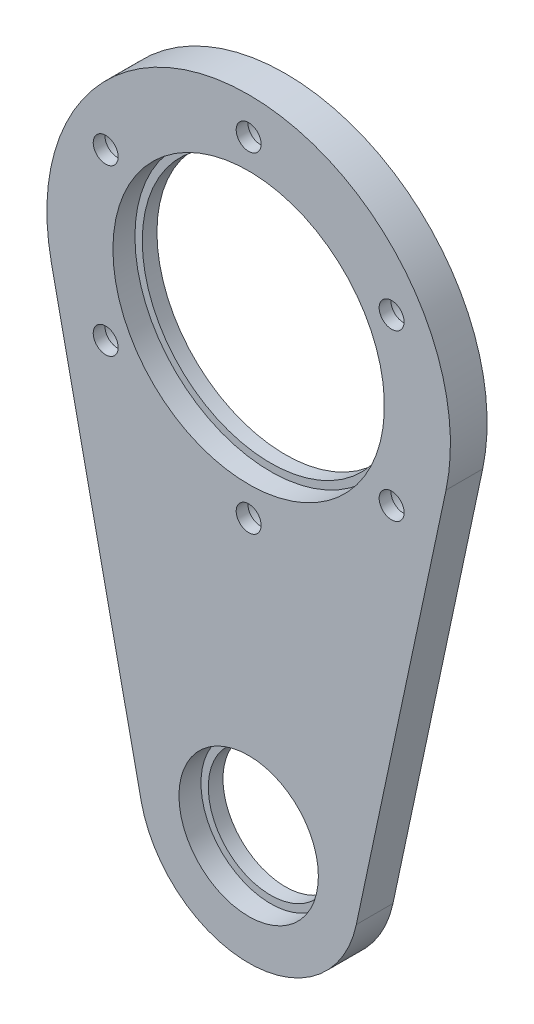
SolidWorks part; units mm, degrees
other "마크업1"
sketch "스케치14" plane through (30, 31, -30.5354) normal (0.2605, 0.9636, -0.0594) x (0.9655, -0.2601, 0.014)
sketch "스케치15" plane through (30, 31, -30.5354) normal (0.2605, 0.9636, -0.0594) x (0.9655, -0.2601, 0.014)
sketch "스케치16" plane through (30, 31, -30.5354) normal (0.2605, 0.9636, -0.0594) x (0.9655, -0.2601, 0.014)
sketch "스케치21" plane through (30, 31, -30.5354) normal (0.2605, 0.9636, -0.0594) x (0.9655, -0.2601, 0.014)
sketch "스케치23" plane through (30, 275, -27) normal (0.2605, 0.9636, -0.0594) x (0.9655, -0.2601, 0.014)
sketch "스케치28" plane through (20, 265, -24) normal (0.2605, 0.9636, -0.0594) x (0.9655, -0.2601, 0.014)
sketch "스케치31" plane through (20, 265, -24) normal (0.2605, 0.9636, -0.0594) x (0.9655, -0.2601, 0.014)
sketch "스케치32" plane through (20, 265, -23) normal (0.2605, 0.9636, -0.0594) x (0.9655, -0.2601, 0.014)
sketch "스케치33" plane through (20, 265, -23) normal (0.2605, 0.9636, -0.0594) x (0.9655, -0.2601, 0.014)
sketch "스케치52" plane through (24, 65, -12) normal (0.2605, 0.9636, -0.0594) x (0.9655, -0.2601, 0.014)
sketch "스케치61" plane through (22.5, 22.5, -13) normal (0.2605, 0.9636, -0.0594) x (0.9655, -0.2601, 0.014)
sketch "스케치64" plane through (22.5, 22.5, -13) normal (0.2605, 0.9636, -0.0594) x (0.9655, -0.2601, 0.014)
sketch "스케치70" plane through (22.5, 22.5, -13) normal (0.2605, 0.9636, -0.0594) x (0.9655, -0.2601, 0.014)
sketch "스케치71" plane through (22.5, 22.5, -13) normal (0.2605, 0.9636, -0.0594) x (0.9655, -0.2601, 0.014)
sketch "스케치72" plane through (22.5, 22.5, -13) normal (0.2605, 0.9636, -0.0594) x (0.9655, -0.2601, 0.014)
sketch "스케치77" plane through (22.5, 22.5, -13) normal (0.2605, 0.9636, -0.0594) x (0.9655, -0.2601, 0.014)
sketch "스케치78" plane through (22.5, 22.5, -13) normal (0.2605, 0.9636, -0.0594) x (0.9655, -0.2601, 0.014)
sketch "스케치79" plane through (25, 25, -13) normal (0.2605, 0.9636, -0.0594) x (0.9655, -0.2601, 0.014)
sketch "스케치81" plane through (25, 25, -13) normal (0.2605, 0.9636, -0.0594) x (0.9655, -0.2601, 0.014)
sketch "스케치84" plane through (25, 25, -13) normal (0.2605, 0.9636, -0.0594) x (0.9655, -0.2601, 0.014)
sketch "스케치90" plane through (27.5, 27.5, -13) normal (0.2605, 0.9636, -0.0594) x (0.9655, -0.2601, 0.014)
sketch "스케치91" plane through (27.5, 27.5, -13) normal (0.2605, 0.9636, -0.0594) x (0.9655, -0.2601, 0.014)
material "7075-T6 (SN)"
ref_plane "정면" through (0, 0, 0) normal (0, 0, 1) x (1, 0, 0)
ref_plane "윗면" through (0, 0, 0) normal (0, 1, 0) x (1, 0, 0)
ref_plane "우측면" through (0, 0, 0) normal (1, 0, 0) x (0, 0, -1)
sketch "스케치2" plane through (0, 6, 0) normal (0, 0, -1) x (1, 0, 0)
  circle A0 centre (0, 6) radius 27.5
  dimension "D1" = 55
extrude "보스-돌출2" add sketch "스케치2" along normal blind 2
sketch "스케치22" plane through (0, 0, 0) normal (0, 0, 1) x (1, 0, 0)
  circle A0 centre (0, 0) radius 10
  dimension "D1" = 20
extrude "컷-돌출1" cut sketch "스케치22" against normal blind 2 contours A0
fillet "필렛4" radius 0.2 1 edges at (10, 0, 0)
sketch "스케치54" plane through (0, 0, -2) normal (0, 0, -1) x (-1, 0, 0)
  circle A4 centre (0, 0) radius 27.5 construction
  circle A5 centre (0, 0) radius 27.5
extrude "보스-돌출6" add sketch "스케치54" along normal blind 11
sketch "스케치55" plane through (0, 0, -13) normal (0, 0, -1) x (-1, 0, 0)
  circle A0 centre (0, 0) radius 18.5
  dimension "D1" = 37
extrude "컷-돌출2" cut sketch "스케치55" against normal blind 8
sketch "스케치56" plane through (0, 0, -5) normal (0, 0, -1) x (-1, 0, 0)
  circle A0 centre (0, 0) radius 6 construction
  point P3 (0, 6)
  dimension "D1" = 12
hole_wizard "M4 육각 소켓 머리 캡 나사용 카운터보어1" positions "스케치57" profile "스케치58" counterbore size "M4" standard "ISO" end condition through all
sketch "스케치57" plane through (0, 0, -5) normal (0, 0, -1) x (-1, 0, 0)
  point P0 (0, 6)
sketch "스케치58" plane through (0, 6, -5) normal (1, 0, 0) x (0, 1, 0)
  line L0 (0, 0) -> (0, 5)
  line L1 (0, 5) -> (2.25, 5)
  line L3 (2.25, 5) -> (2.25, 1)
  line L4 (2.25, 1) -> (4, 1)
  line L5 (4, 1) -> (4, 0)
  line L7 (4, 0) -> (0, 0)
  line L11 (0, -6.35) -> (0, 107.95) construction
  dimension "관통 구멍 지름" = 4.5
  dimension "관통 구멍 깊이" = 5
  dimension "카운터보어 지름" = 8
  dimension "카운터보어 깊이" = 1
pattern_circular "원형 패턴1" count 3 over 360 about axis through (0, 0, 0) along (0, 0, 1) of "M4 육각 소켓 머리 캡 나사용 카운터보어1"
sketch "스케치59" plane through (0, 0, -5) normal (0, 0, -1) x (-1, 0, 0)
  circle A0 centre (0, 0) radius 17.5
  circle A1 centre (0, 0) radius 18.5 construction
  circle A2 centre (0, 0) radius 18.5
  dimension "D1" = 35
extrude "보스-돌출7" add sketch "스케치59" along normal blind 1
sketch "스케치60" plane through (0, 0, -13) normal (0, 0, -1) x (-1, 0, 0)
  line L0 (-26.8966, -5.7292) -> (-14.6709, -63.125)
  line L1 (0, 0) -> (0, -60) construction
  line L2 (26.8966, -5.7292) -> (14.6709, -63.125)
  circle A0 centre (0, 0) radius 27.5 construction
  arc A1 (-14.6709, -63.125) -> (14.6709, -63.125) centre (0, -60) ccw
  arc A2 (-26.8966, -5.7292) -> (26.8966, -5.7292) centre (0, 0) ccw
  dimension "D2" = 30
  dimension "D1" = 60
extrude "보스-돌출8" add sketch "스케치60" against normal blind 9
fillet "필렛6" radius 0.3 1 edges at (-18.5, 0, -6)
sketch "스케치68" plane through (0, 0, -4) normal (0, 0, 1) x (1, 0, 0)
  circle A0 centre (0, -60) radius 9.5
  dimension "D1" = 19
extrude "컷-돌출7" cut sketch "스케치68" against normal blind 7
sketch "스케치69" plane through (0, 0, -11) normal (0, 0, 1) x (1, 0, 0)
  circle A0 centre (0, -60) radius 8.5
  dimension "D1" = 17
extrude "컷-돌출8" cut sketch "스케치69" against normal through all
sketch "스케치80" plane through (0, 0, 0) normal (0, 1, 0) x (1, 0, 0)
  line L1 (-35.5676, -9.19) -> (36.4613, -9.19)
  line L2 (-35.5676, -9.19) -> (-35.5676, 8)
  line L3 (-35.5676, 8) -> (36.4613, 8)
  line L4 (36.4613, -9.19) -> (36.4613, 8)
  line L5 (27.5, 13) -> (-27.5, 13) construction
  dimension "D1" = 5
extrude "컷-돌출9" cut sketch "스케치80" against normal mid plane 353
sketch "스케치83" plane through (0, 0, -13) normal (0, 0, -1) x (-1, 0, 0)
  circle A0 centre (0, 0) radius 18.5
  circle A1 centre (0, 0) radius 18.5 construction
  circle A2 centre (0, 0) radius 17.5
  dimension "D1" = 35
extrude "보스-돌출9" add sketch "스케치83" against normal blind 2
sketch "스케치85" plane through (0, 0, -13) normal (0, 0, -1) x (-1, 0, 0)
  circle A0 centre (0, 0) radius 22.5 construction
  circle A1 centre (0, 0) radius 17.5 construction
  point P4 (0, 22.5)
  dimension "D1" = 45
hole_wizard "M3 육각 소켓 머리 캡 나사용 카운터보어1" positions "스케치88" profile "스케치89" counterbore size "M3" standard "ISO"
sketch "스케치88" plane through (0, 0, -13) normal (0, 0, -1) x (-1, 0, 0)
  point P0 (0, 22.5)
sketch "스케치89" plane through (0, 22.5, -13) normal (1, 0, 0) x (0, 1, 0)
  line L0 (0, 0) -> (0, 223.0215)
  line L1 (0, 223.0215) -> (1.7, 222)
  line L2 (1.7, 222) -> (1.7, 3.4)
  line L3 (1.7, 3.4) -> (3.25, 3.4)
  line L4 (3.25, 3.4) -> (3.25, 0)
  line L5 (3.25, 0) -> (0, 0)
  line L10 (0, 223.0215) -> (-1.7, 222) construction
  line L11 (0, -6.35) -> (0, 107.95) construction
  dimension "구멍 지름" = 3.4
  dimension "구멍 깊이" = 222
  dimension "카운터보어 지름" = 6.5
  dimension "카운터보어 깊이" = 3.4
  dimension "드릴 각도" = 118
pattern_circular "원형 패턴2" count 6 over 360 about axis through (0, 0, 0) along (0, 0, 1) of "M3 육각 소켓 머리 캡 나사용 카운터보어1"
